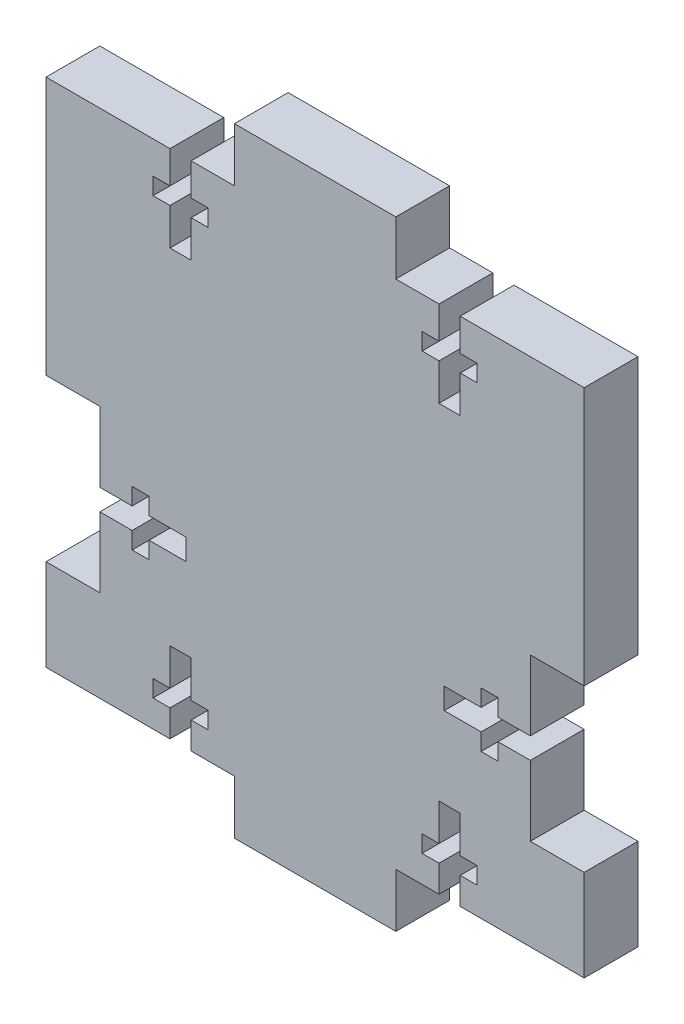
SolidWorks part; units mm, degrees
ref_plane "Front Plane" through (0, 0, 0) normal (0, 0, 1) x (1, 0, 0)
ref_plane "Top Plane" through (0, 0, 0) normal (0, 1, 0) x (1, 0, 0)
ref_plane "Right Plane" through (0, 0, 0) normal (1, 0, 0) x (0, 0, -1)
sketch "Sketch1" plane through (0, 0, 0) normal (0, 0, 1) x (1, 0, 0)
  line L0 (9.525, 66.675) -> (9.525, -6.35) construction
  line L1 (0, -6.35) -> (19.05, -6.35)
  line L2 (-15.875, 29.845) -> (-15.875, 21.57)
  line L3 (0, 66.675) -> (19.05, 66.675)
  line L4 (34.925, 29.845) -> (34.925, 21.57)
  line L5 (-22.225, 29.845) -> (-15.875, 29.845)
  line L6 (41.275, 29.845) -> (34.925, 29.845)
  line L7 (-15.875, 60.325) -> (-7.6, 60.325)
  line L8 (0, 66.675) -> (0, 60.325)
  line L9 (-22.225, 10.795) -> (-15.875, 10.795)
  line L10 (41.275, 10.795) -> (34.925, 10.795)
  line L11 (34.925, 60.325) -> (26.65, 60.325)
  line L12 (19.05, 66.675) -> (19.05, 60.325)
  line L13 (-15.875, 20.32) -> (-5.715, 20.32) construction
  line L14 (-15.875, 21.57) -> (-12.065, 21.57)
  line L15 (-15.875, 0) -> (-7.6, 0)
  line L16 (0, -6.35) -> (0, 0)
  line L17 (34.925, 19.07) -> (31.115, 19.07)
  line L18 (-15.875, 19.07) -> (-12.065, 19.07)
  line L19 (34.925, 0) -> (26.65, 0)
  line L20 (19.05, -6.35) -> (19.05, 0)
  line L21 (-5.715, 21.57) -> (-5.715, 19.07)
  line L22 (-10.065, 21.57) -> (-5.715, 21.57)
  line L23 (-15.875, 60.325) -> (-22.225, 60.325)
  line L24 (-10.065, 19.07) -> (-5.715, 19.07)
  line L25 (-12.065, 21.57) -> (-12.065, 23.57)
  line L26 (-22.225, 60.325) -> (-22.225, 29.845)
  line L27 (-12.065, 23.57) -> (-10.065, 23.57)
  line L28 (-10.065, 21.57) -> (-10.065, 23.57)
  line L29 (-22.225, 10.795) -> (-22.225, 0)
  line L30 (-22.225, 0) -> (-15.875, 0)
  line L31 (-15.875, 19.07) -> (-15.875, 10.795)
  line L32 (34.925, 0) -> (41.275, 0)
  line L33 (-12.065, 19.07) -> (-12.065, 17.07)
  line L34 (-12.065, 17.07) -> (-10.065, 17.07)
  line L35 (41.275, 0) -> (41.275, 10.795)
  line L36 (41.275, 29.845) -> (41.275, 60.325)
  line L37 (41.275, 60.325) -> (34.925, 60.325)
  line L38 (-10.065, 19.07) -> (-10.065, 17.07)
  line L39 (31.115, 19.07) -> (31.115, 17.07)
  line L40 (31.115, 17.07) -> (29.115, 17.07)
  line L41 (29.115, 19.07) -> (29.115, 17.07)
  line L42 (29.115, 19.07) -> (24.765, 19.07)
  line L43 (34.925, 20.32) -> (24.765, 20.32) construction
  line L44 (24.765, 21.57) -> (24.765, 19.07)
  line L45 (29.115, 21.57) -> (24.765, 21.57)
  line L46 (29.115, 21.57) -> (29.115, 23.57)
  line L47 (31.115, 23.57) -> (29.115, 23.57)
  line L48 (31.115, 21.57) -> (31.115, 23.57)
  line L49 (34.925, 21.57) -> (31.115, 21.57)
  line L50 (34.925, 19.07) -> (34.925, 10.795)
  line L51 (-7.6, 54.515) -> (-7.6, 50.165)
  line L52 (24.15, 60.325) -> (19.05, 60.325)
  line L53 (-7.6, 60.325) -> (-7.6, 56.515)
  line L54 (-7.6, 50.165) -> (-5.1, 50.165)
  line L55 (-5.1, 60.325) -> (-5.1, 56.515)
  line L56 (26.65, 0) -> (26.65, 3.175)
  line L57 (24.15, 60.325) -> (24.15, 56.515)
  line L58 (24.15, 50.165) -> (26.65, 50.165)
  line L59 (26.65, 60.325) -> (26.65, 56.515)
  line L60 (-9.6, 56.515) -> (-7.6, 56.515)
  line L61 (-9.6, 56.515) -> (-9.6, 54.515)
  line L62 (-9.6, 54.515) -> (-7.6, 54.515)
  line L63 (-5.1, 54.515) -> (-5.1, 50.165)
  line L64 (-5.1, 56.515) -> (-3.1, 56.515)
  line L65 (24.15, 54.515) -> (24.15, 50.165)
  line L66 (-5.1, 54.515) -> (-3.1, 54.515)
  line L67 (-3.1, 56.515) -> (-3.1, 54.515)
  line L68 (22.15, 56.515) -> (24.15, 56.515)
  line L69 (22.15, 56.515) -> (22.15, 54.515)
  line L70 (22.15, 54.515) -> (24.15, 54.515)
  line L71 (26.65, 54.515) -> (26.65, 50.165)
  line L72 (26.65, 56.515) -> (28.65, 56.515)
  line L73 (-6.35, 60.325) -> (-6.35, 50.165) construction
  line L74 (26.65, 54.515) -> (28.65, 54.515)
  line L75 (28.65, 56.515) -> (28.65, 54.515)
  line L76 (25.4, 60.325) -> (25.4, 50.165) construction
  line L77 (-5.1, 60.325) -> (0, 60.325)
  line L78 (26.65, 3.175) -> (28.65, 3.175)
  line L79 (28.65, 3.175) -> (28.65, 5.175)
  line L80 (26.65, 5.175) -> (28.65, 5.175)
  line L81 (26.65, 5.175) -> (26.65, 9.525)
  line L82 (24.15, 9.525) -> (26.65, 9.525)
  line L83 (24.15, 5.175) -> (24.15, 9.525)
  line L84 (22.15, 5.175) -> (24.15, 5.175)
  line L85 (22.15, 3.175) -> (22.15, 5.175)
  line L86 (22.15, 3.175) -> (24.15, 3.175)
  line L87 (24.15, 0) -> (24.15, 3.175)
  line L88 (-5.1, 3.175) -> (-3.1, 3.175)
  line L89 (-5.1, 5.175) -> (-3.1, 5.175)
  line L90 (-3.1, 3.175) -> (-3.1, 5.175)
  line L91 (-5.1, 5.175) -> (-5.1, 9.525)
  line L92 (-7.6, 9.525) -> (-5.1, 9.525)
  line L93 (-7.6, 5.175) -> (-7.6, 9.525)
  line L94 (-9.6, 5.175) -> (-7.6, 5.175)
  line L95 (-9.6, 3.175) -> (-9.6, 5.175)
  line L96 (-9.6, 3.175) -> (-7.6, 3.175)
  line L97 (-5.1, 0) -> (-5.1, 3.175)
  line L98 (-7.6, 0) -> (-7.6, 3.175)
  line L99 (-5.1, 0) -> (0, 0)
  line L100 (24.15, 0) -> (19.05, 0)
  point P94 (-6.35, 0)
  point P108 (25.4, 0)
  dimension "D1" = 73.025
  dimension "D2" = 6.35
  dimension "D3" = 19.05
  dimension "D4" = 6.35
  dimension "D5" = 6.35
  dimension "D6" = 19.05
  dimension "D7" = 15.875
  dimension "D8" = 30.48
  dimension "D9" = 2.5
  dimension "D10" = 2
  dimension "D11" = 3.81
  dimension "D12" = 10.16
  dimension "D13" = 6.35
  dimension "D14" = 6.35
extrude "Boss-Extrude1" add sketch "Sketch1" along normal blind 6.35 contours L7 L53 L60 L61 L62 L51 L54 L63 L66 L67 L64 L55 L77 L8 L3 L12 L52 L57 L68 L69 L70 L65 L58 L71 L74 L75 L72 L59 L11 L37 L36 L6 L4 L49 L48 L47 L46 L45 L44 L42 L41 L40 L39 L17 L50 L10 L35 L32 L19 L56 L78 L79 L80 L81 L82 L83 L84 L85 L86 L87 L100 L20 L1 L16 L99 L97 L88 L90 L89 L91 L92 L93 L94 L95 L96 L98 L15 L30 L29 L9 L31 L18 L33 L34 L38 L24 L21 L22 L28 L27 L25 L14 L2 L5 L26 L23
